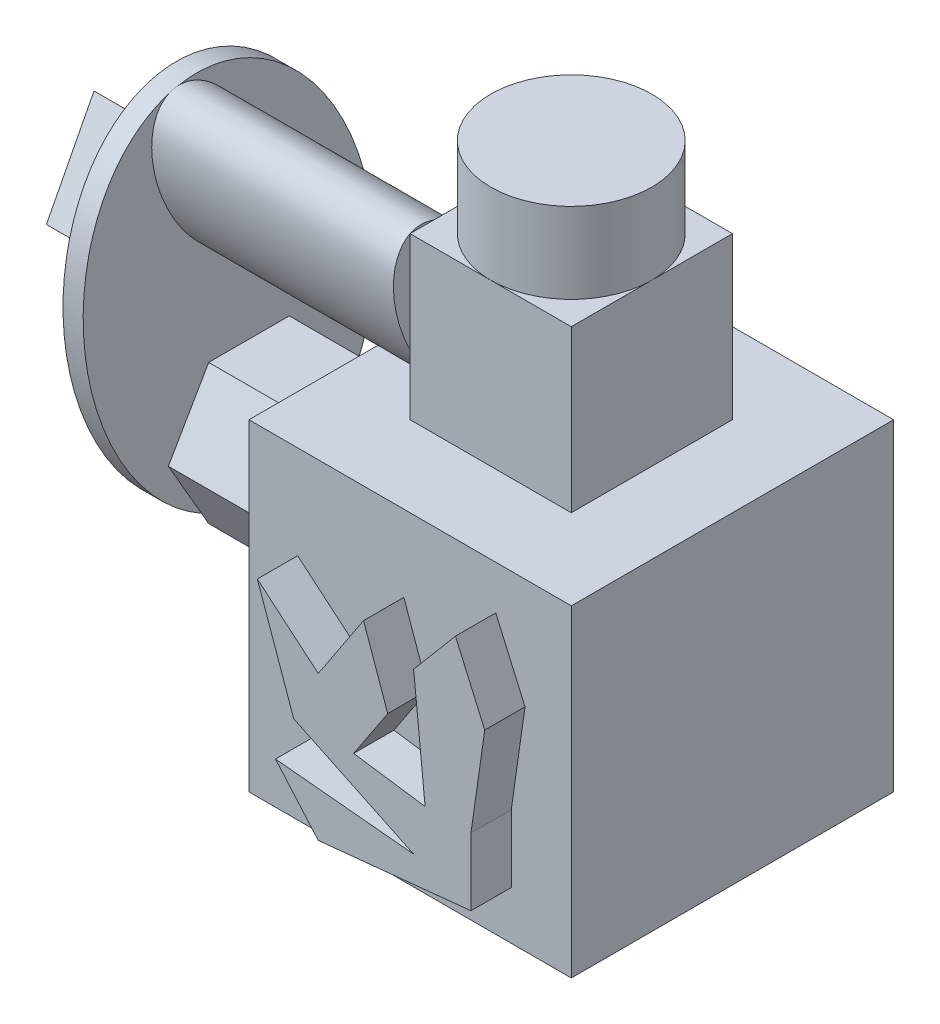
SolidWorks part; units mm, degrees
ref_plane "Front Plane" through (0, 0, 0) normal (0, 0, 1) x (1, 0, 0)
ref_plane "Top Plane" through (0, 0, 0) normal (0, 1, 0) x (1, 0, 0)
ref_plane "Right Plane" through (0, 0, 0) normal (1, 0, 0) x (0, 0, -1)
sketch "Sketch1" plane through (0, 0, 0) normal (0, 1, 0) x (1, 0, 0)
  line L1 (0, 0) -> (25.4, 0)
  line L2 (0, 0) -> (0, -25.4)
  line L3 (0, -25.4) -> (25.4, -25.4)
  line L4 (25.4, 0) -> (25.4, -25.4)
  dimension "D1" = 25.4
  dimension "D2" = 25.4
extrude "Boss-Extrude1" add sketch "Sketch1" along normal blind 25.4
sketch "Sketch2" plane through (0, 25.4, 0) normal (0, 1, 0) x (1, 0, 0)
  line L1 (19.05, -19.05) -> (6.35, -19.05)
  line L2 (19.05, -19.05) -> (19.05, -6.35)
  line L3 (19.05, -6.35) -> (12.7, -6.35)
  line L4 (6.35, -19.05) -> (6.35, -12.7)
  line L6 (0, -25.4) -> (25.4, -25.4) construction
  line L7 (25.4, -25.4) -> (25.4, 0) construction
  arc A0 (6.35, -12.7) -> (12.7, -6.35) centre (12.7, -12.7) cw
  dimension "D1" = 12.7
  dimension "D2" = 12.7
  dimension "D3" = 6.35
  dimension "D4" = 6.35
  dimension "D5" = 6.35
  dimension "D6" = 6.35
extrude "Boss-Extrude2" add sketch "Sketch2" along normal blind 12.7 contours A0 L4 L1 L2 L3
sketch "Sketch3" plane through (0, 38.1, 0) normal (0, 1, 0) x (1, 0, 0)
  circle A0 centre (12.7, -12.7) radius 6.35
extrude "Boss-Extrude3" add sketch "Sketch3" along normal blind 6.35
sketch "Sketch4" plane through (6.35, 0, 0) normal (-1, 0, 0) x (0, 0, 1)
  ellipse E0 centre (15.875, 31.75) end of major axis (19.05, 38.1) minor radius 3.5498
extrude "Boss-Extrude4" add sketch "Sketch4" along normal blind 19.05
sketch "Sketch5" plane through (0, 0, 0) normal (-1, 0, 0) x (0, 0, 1)
  line L0 (0, 25.4) -> (25.4, 0)
  line L2 (6.35, 12.7) -> (9.525, 7.2007)
  line L3 (9.525, 7.2007) -> (15.875, 7.2007)
  line L4 (15.875, 7.2007) -> (19.05, 12.7)
  line L5 (19.05, 12.7) -> (15.875, 18.1993)
  line L6 (15.875, 18.1993) -> (9.525, 18.1993)
  line L7 (9.525, 18.1993) -> (6.35, 12.7)
  circle A0 centre (12.7, 12.7) radius 6.35 construction
extrude "Boss-Extrude5" add sketch "Sketch5" along normal blind 12.7 contours L6 L7 L0 L4 L5 | L0 L7 L2 L3 L4
sketch "Sketch6" plane through (-12.7, 0, 0) normal (-1, 0, 0) x (0, 0, 1)
  ellipse E1 centre (14.2875, 22.6504) end of major axis (19.05, 38.1) minor radius 10.9298
extrude "Boss-Extrude6" add sketch "Sketch6" along normal blind 1.5875
sketch "Sketch7" plane through (-14.2875, 0, 0) normal (-1, 0, 0) x (0, 0, 1)
  line L0 (4.5714, 23.6293) -> (3.733, 22.2745)
  line L1 (9.8201, 15.5916) -> (8.4526, 14.0021)
  line L2 (8.4526, 14.0021) -> (8.6096, 11.9112)
  line L3 (8.6096, 11.9112) -> (10.199, 10.5437)
  line L4 (10.199, 10.5437) -> (12.2899, 10.7007)
  line L5 (12.2899, 10.7007) -> (13.6574, 12.2902)
  line L6 (13.6574, 12.2902) -> (13.5005, 14.3811)
  line L7 (13.5005, 14.3811) -> (11.911, 15.7486)
  line L8 (11.911, 15.7486) -> (9.8201, 15.5916)
  line L9 (11.911, 27.7035) -> (12.4401, 25.0287)
  line L10 (12.4401, 25.0287) -> (15.1476, 24.7053)
  line L11 (15.1476, 24.7053) -> (16.2918, 27.1804)
  line L12 (16.2918, 27.1804) -> (14.2914, 29.0334)
  line L13 (14.2914, 29.0334) -> (11.911, 27.7035)
  line L14 (9.6274, 20.5002) -> (9.6761, 22.0927)
  line L15 (9.6761, 22.0927) -> (8.9221, 23.4962)
  line L16 (8.9221, 23.4962) -> (7.5673, 24.3346)
  line L17 (7.5673, 24.3346) -> (5.9749, 24.3833)
  line L18 (5.9749, 24.3833) -> (4.5714, 23.6293)
  line L19 (3.733, 22.2745) -> (3.6843, 20.6821)
  line L20 (3.6843, 20.6821) -> (4.4383, 19.2786)
  line L21 (4.4383, 19.2786) -> (5.7931, 18.4402)
  line L22 (5.7931, 18.4402) -> (7.3855, 18.3914)
  line L23 (7.3855, 18.3914) -> (8.789, 19.1455)
  line L24 (8.789, 19.1455) -> (9.6274, 20.5002)
  line L26 (17.0031, 23.4962) -> (13.132, 22.8332)
  line L27 (13.132, 22.8332) -> (11.2368, 19.3933)
  line L28 (11.2368, 19.3933) -> (12.7445, 15.7668)
  line L29 (12.7445, 15.7668) -> (16.5199, 14.6845)
  line L30 (16.5199, 14.6845) -> (19.72, 16.9614)
  line L31 (19.72, 16.9614) -> (19.9351, 20.883)
  line L32 (19.9351, 20.883) -> (17.0031, 23.4962)
  line L33 (15.7559, 29.6151) -> (23.8997, 29.2436)
  line L34 (23.8997, 29.2436) -> (20.1495, 36.4821)
  line L35 (20.1495, 36.4821) -> (15.7559, 29.6151)
  circle A0 centre (11.055, 13.1462) radius 2.531 construction
  circle A1 centre (14.0164, 26.7303) radius 1.8765 construction
  circle A2 centre (6.6802, 21.3874) radius 2.973 construction
  circle A3 centre (15.7559, 19.1455) radius 4.0777 construction
  circle A4 centre (19.9351, 31.7803) radius 2.3534 construction
extrude "Boss-Extrude7" add sketch "Sketch7" along normal blind 3.175
sketch "Sketch8" plane through (0, 0, 25.4) normal (0, 0, 1) x (1, 0, 0)
  line L0 (16.1522, 5.4136) -> (6.6976, 9.9346)
  line L1 (6.6976, 9.9346) -> (3.8371, 18.0377)
  line L2 (3.8371, 18.0377) -> (8.6349, 13.9862)
  line L3 (8.6349, 13.9862) -> (12.2052, 19.383)
  line L4 (12.2052, 19.383) -> (14.1104, 13.9862)
  line L5 (14.1104, 13.9862) -> (11.4249, 9.9268)
  line L6 (11.4249, 9.9268) -> (17.0561, 9.1194)
  line L7 (17.0561, 9.1194) -> (16.1522, 18.0377)
  line L8 (16.1522, 18.0377) -> (19.4469, 21.9394)
  line L9 (19.4469, 21.9394) -> (21.7544, 16.6846)
  line L10 (21.7544, 16.6846) -> (20.6698, 9.1194)
  line L11 (20.6698, 9.1194) -> (20.6698, 3.8108)
  line L12 (20.6698, 3.8108) -> (8.6349, 2.591)
  line L13 (8.6349, 2.591) -> (5.2673, 6.4651)
  line L14 (5.2673, 6.4651) -> (16.1522, 5.4136)
extrude "Boss-Extrude8" add sketch "Sketch8" along normal blind 3.175
